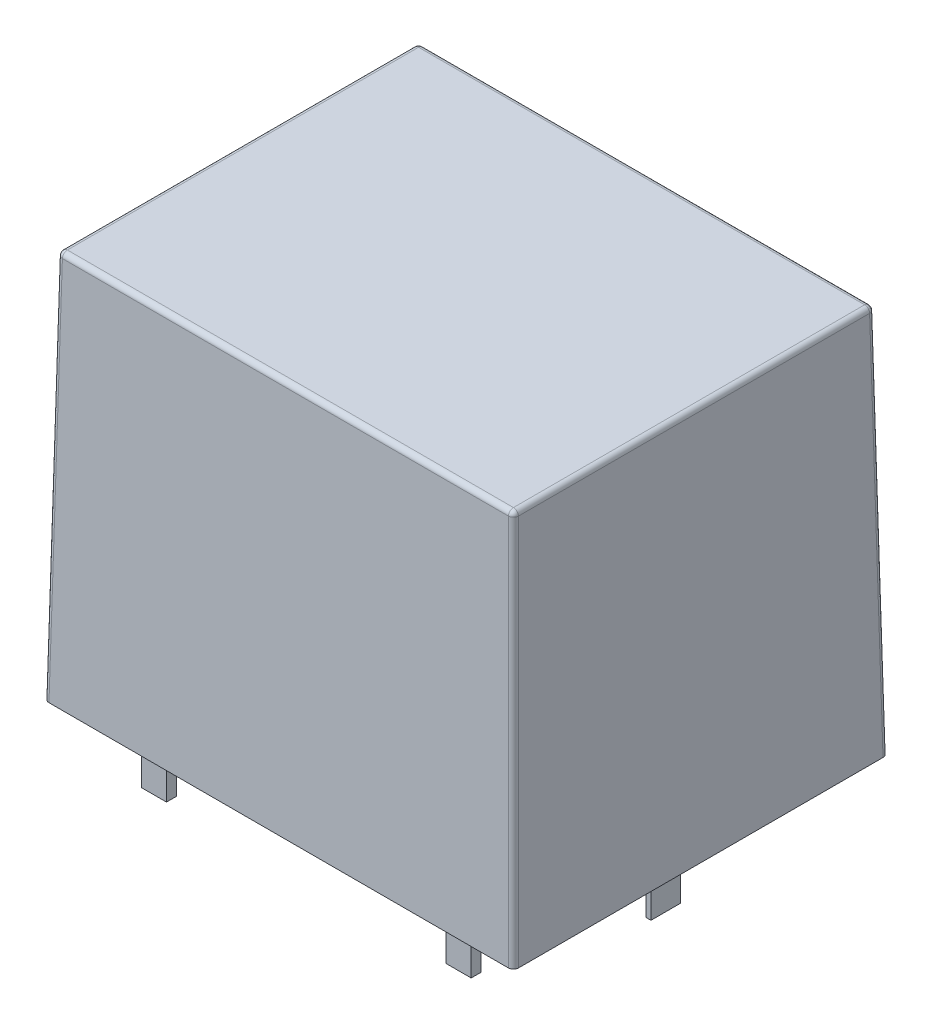
SolidWorks part; units mm, degrees
material "ABS"
ref_plane "Front Plane" through (0, 0, 0) normal (0, 0, 1) x (1, 0, 0)
ref_plane "Top Plane" through (0, 0, 0) normal (0, 1, 0) x (1, 0, 0)
ref_plane "Right Plane" through (0, 0, 0) normal (1, 0, 0) x (0, 0, -1)
sketch "Sketch1" plane through (0, 0, 0) normal (0, 1, 0) x (1, 0, 0)
  line L0 (9.4, -8.1067) -> (-9.4, -8.1067)
  line L1 (9.4, -8.1067) -> (9.4, 6.8933)
  line L2 (9.4, 6.8933) -> (-9.4, 6.8933)
  line L3 (-9.4, -8.1067) -> (-9.4, 6.8933)
  line L4 (9.4, -8.1067) -> (-9.4, 6.8933) construction
  line L5 (9.4, 6.8933) -> (-9.4, -8.1067) construction
  point P0 (0, -0.6067)
  dimension "D1" = 18.8
  dimension "D2" = 15
extrude "Boss-Extrude1" add sketch "Sketch1" along normal blind 15.6 draft 1
fillet "Fillet1" radius 0.2 8 edges at (0, 15.6, -6.621) (9.1277, 15.6, 0.6067) (0, 15.6, 7.8344) (-9.1277, 15.6, 0.6067) (-9.2639, 7.8, -6.7572) (9.2639, 7.8, -6.7572) (-9.2639, 7.8, 7.9705) (9.2639, 7.8, 7.9705)
ref_plane "Plane1" through (0, 0, 0) normal (0, -1, 0) x (-1, 0, 0)
sketch "Sketch2" plane through (0, 0, 0) normal (0, -1, 0) x (-1, 0, 0)
  line L0 (-4.8, -5.8) -> (-5.8, -5.8)
  line L1 (-4.8, -5.8) -> (-4.8, -6.2)
  line L2 (-4.8, -6.2) -> (-5.8, -6.2)
  line L3 (-5.8, -5.8) -> (-5.8, -6.2)
  line L4 (-7.4, -0.6) -> (-7.2, -0.6)
  line L5 (-7.4, -0.6) -> (-7.4, 0.5909)
  line L6 (-7.4, 0.5909) -> (-7.2, 0.5909)
  line L7 (-7.2, -0.6) -> (-7.2, 0.5909)
  line L8 (6.4, -6.2) -> (7.4, -6.2)
  line L9 (6.4, -6.2) -> (6.4, -5.8)
  line L10 (6.4, -5.8) -> (7.4, -5.8)
  line L11 (7.4, -6.2) -> (7.4, -5.8)
  line L12 (-5.8, 5.7462) -> (-4.8, 5.7462)
  line L13 (-5.8, 5.7462) -> (-5.8, 6.2)
  line L14 (-5.8, 6.2) -> (-4.8, 6.2)
  line L15 (-4.8, 5.7462) -> (-4.8, 6.2)
  line L16 (7.4, 6.2) -> (6.4, 6.2)
  line L17 (7.4, 6.2) -> (7.4, 5.8)
  line L18 (7.4, 5.8) -> (6.4, 5.8)
  line L19 (6.4, 6.2) -> (6.4, 5.8)
extrude "Boss-Extrude2" add sketch "Sketch2" along normal blind 3
